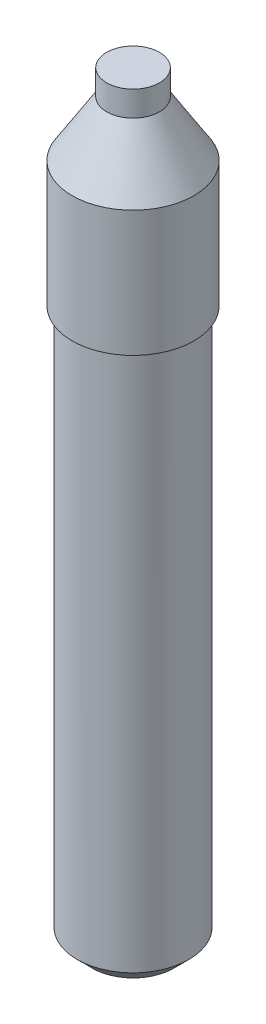
SolidWorks part; units mm, degrees
material "Plain Carbon Steel"
ref_plane "Front Plane" through (0, 0, 0) normal (0, 0, 1) x (1, 0, 0)
ref_plane "Top Plane" through (0, 0, 0) normal (0, 1, 0) x (1, 0, 0)
ref_plane "Right Plane" through (0, 0, 0) normal (1, 0, 0) x (0, 0, -1)
sketch "Sketch3" plane through (0, 0, 0) normal (0, 0, 1) x (1, 0, 0)
  line L0 (-11.1125, -151) -> (-11.1125, -41)
  line L1 (-11.1125, -41) -> (-12.1125, -41)
  line L2 (-12.1125, -41) -> (-12.1125, -16)
  line L3 (-12.1125, -16) -> (-5.25, -5)
  line L4 (-11.1125, -151) -> (0, -151)
  line L5 (0, -151) -> (0, 0)
  line L6 (-5.25, -5) -> (-5.25, 0)
  line L7 (-5.25, 0) -> (0, 0)
  dimension "D1" = 110
  dimension "D2" = 1
  dimension "D3" = 25
  dimension "D4" = 11
  dimension "D5" = 11.1125
  dimension "D6" = 5.25
  dimension "D7" = 5
revolve "Revolve1" add sketch "Sketch3" angle 360 about L5
sketch "Sketch4" plane through (0, -151, 0) normal (0, -1, 0) x (1, 0, 0)
  circle A0 centre (0, 0) radius 7.9375
  dimension "D1" = 15.875
extrude "Cut-Extrude2" cut sketch "Sketch4" against normal blind 101.6
chamfer "Chamfer2" distance 3 angle 45 1 edges at (11.1125, -151, 0)
sketch "Sketch5" plane through (0, 0, 0) normal (0, 0, 1) x (1, 0, 0)
  line L0 (0, 0) -> (0, -212) construction
  dimension "D1" = 212
